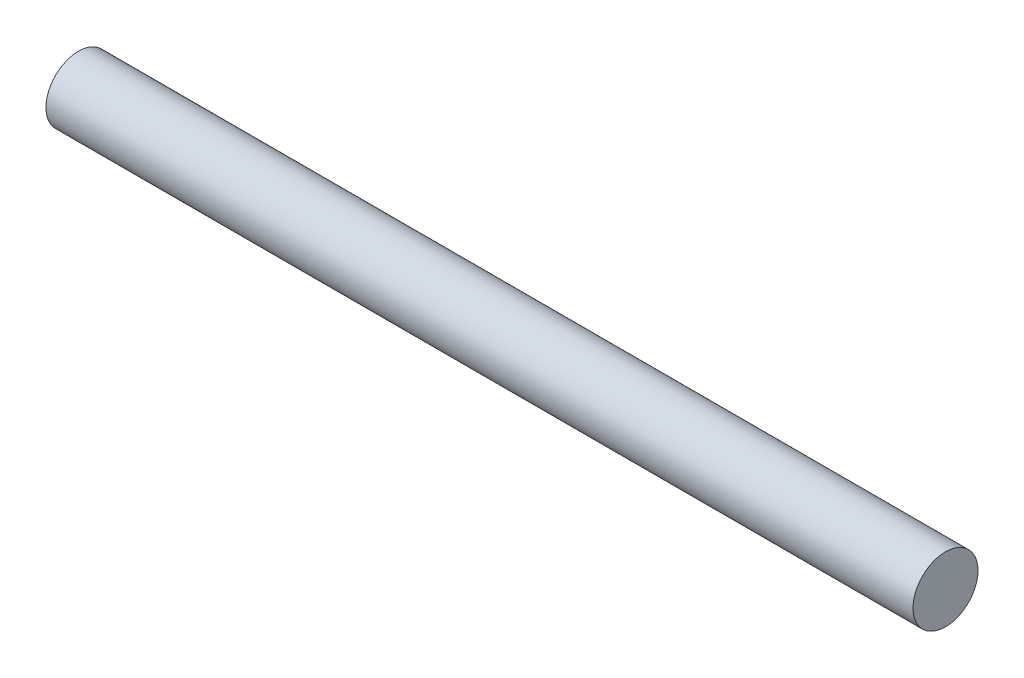
SolidWorks part; units mm, degrees
ref_plane "Front Plane" through (0, 0, 0) normal (0, 0, 1) x (1, 0, 0)
ref_plane "Top Plane" through (0, 0, 0) normal (0, 1, 0) x (1, 0, 0)
ref_plane "Right Plane" through (0, 0, 0) normal (1, 0, 0) x (0, 0, -1)
sketch "Sketch1" plane through (0, 0, 0) normal (1, 0, 0) x (0, 0, -1)
  circle A0 centre (0, 0) radius 9.525
  dimension "D1" = 19.05
extrude "Boss-Extrude1" add sketch "Sketch1" along normal mid plane 254
